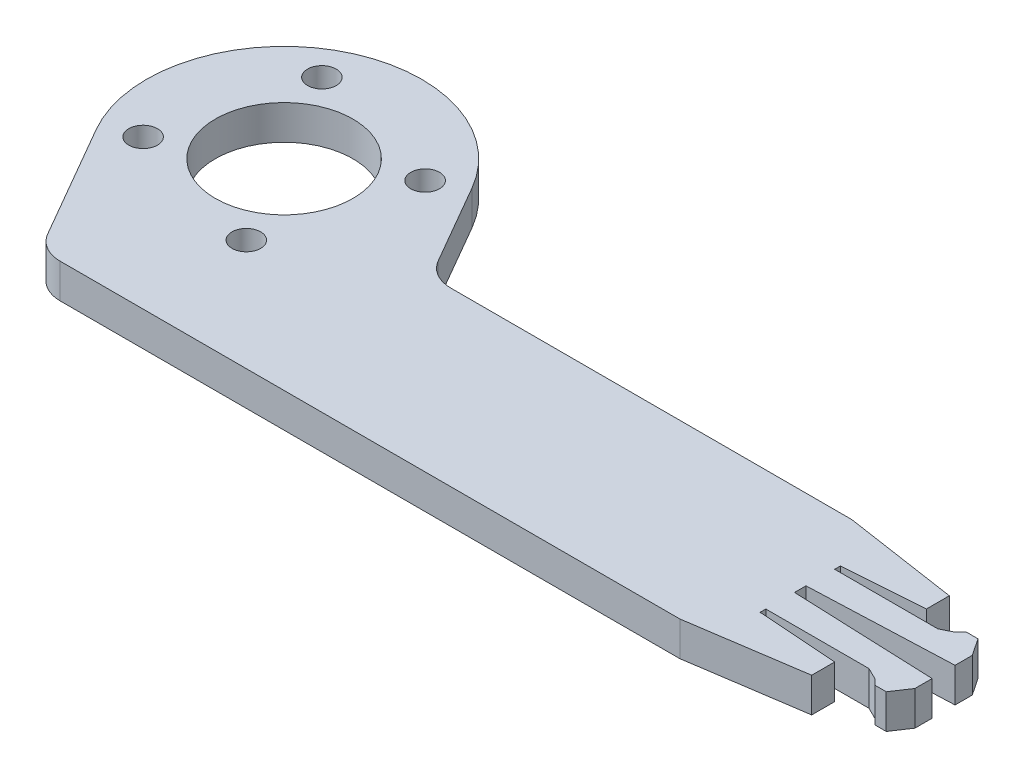
SolidWorks part; units mm, degrees
material "Lasercut ABS"
ref_plane "Front Plane" through (0, 0, 0) normal (0, 0, 1) x (1, 0, 0)
ref_plane "Top Plane" through (0, 0, 0) normal (0, 1, 0) x (1, 0, 0)
ref_plane "Right Plane" through (0, 0, 0) normal (1, 0, 0) x (0, 0, -1)
sketch "Sketch1" plane through (0, 0, 0) normal (0, 1, 0) x (1, 0, 0)
  line L0 (0, 0) -> (0, -10) construction
  line L1 (-4.5, 7.7942) -> (4.5, -7.7942) construction
  line L2 (-7.7942, -4.5) -> (7.7942, 4.5) construction
  line L3 (10.3923, 6) -> (15.2998, -2.5)
  line L4 (15.2998, -2.5) -> (52, -2.5)
  line L5 (-10.3923, -6) -> (-3.7528, -17.5)
  line L6 (-3.7528, -17.5) -> (52, -17.5)
  circle A0 centre (0, 0) radius 6
  circle A1 centre (0, 0) radius 9 construction
  circle A2 centre (7.7942, 4.5) radius 1.25
  circle A3 centre (-4.5, 7.7942) radius 1.25
  circle A4 centre (-7.7942, -4.5) radius 1.25
  circle A5 centre (4.5, -7.7942) radius 1.25
  arc A6 (10.3923, 6) -> (-10.3923, -6) centre (0, 0) ccw
  line B0 (52, -10) -> (55, -10) construction
  line B1 (55, -9.5) -> (55, -10.5)
  line B2 (55, -9.5) -> (67.5, -9)
  line B3 (67.5, -9) -> (67.5, -7.5)
  line B4 (67.5, -7.5) -> (66.5, -6)
  line B5 (66.5, -6) -> (65.5, -6)
  line B6 (65.5, -6) -> (65, -6.5)
  line B7 (65, -6.5) -> (64, -7)
  line B8 (64, -7) -> (55, -7)
  line B9 (55, -7) -> (55, -6.5)
  line B10 (55, -6.5) -> (62, -6)
  line B11 (62, -6) -> (62, -4)
  line B12 (62, -4) -> (52, -2.5)
  line B13 (55, -10.5) -> (67.5, -11)
  line B14 (67.5, -11) -> (67.5, -12.5)
  line B15 (67.5, -12.5) -> (66.5, -14)
  line B16 (66.5, -14) -> (65.5, -14)
  line B17 (65.5, -14) -> (65, -13.5)
  line B18 (65, -13.5) -> (64, -13)
  line B19 (64, -13) -> (55, -13)
  line B20 (55, -13) -> (55, -13.5)
  line B21 (55, -13.5) -> (62, -14)
  line B22 (62, -14) -> (62, -16)
  line B23 (62, -16) -> (52, -17.5)
  dimension "D1" = 12
  dimension "D5" = 18
  dimension "D6" = 2.5
  dimension "D7" = 24
  dimension "D2" = 10
  dimension "D3" = 62
  dimension "D4" = 30
sketch_block_instance "Block-Snap-Textile-1"
sketch_block "Block-Snap-Textile" parameters "D1"=3, "D2"=1, "D3"=2, "D4"=1.5, "D5"=10, "D6"=0.5, "D7"=9, "D8"=1, "D9"=0.5, "D10"=0.5, "D11"=0.5, "D12"=1, "D13"=12.5, "D14"=0.5, "D15"=0.5, "D16"=1.5, "D17"=1.5
extrude "Boss-Extrude1" add sketch "Sketch1" along normal mid plane 3 contours B23 B22 B21 B20 B19 B18 B17 B16 B15 B14 B13 B1 B2 B3 B4 B5 B6 B7 B8 B9 B10 B11 B12 L4 L3 A6 L5 L6 A5 A4 A3 A2 A0
fillet "Fillet1" radius 3 2 edges at (15.2998, 0, 2.5) (-3.7528, 0, 17.5)
sketch "Sketch2" plane through (0, -1.5, 0) normal (0, -1, 0) x (1, 0, 0)
  line L0 (28, 9) -> (12, 9) construction
  line L1 (28, 12.5) -> (12, 12.5) construction
  text T0 "EB6" font "1CamBam_Stick_3" height 2.5
  text T1 "ONO V2" font "1CamBam_Stick_3" height 2.5
  dimension "D1" = 3.5
  dimension "D2" = 16
  dimension "D3" = 12
  dimension "D4" = 9
